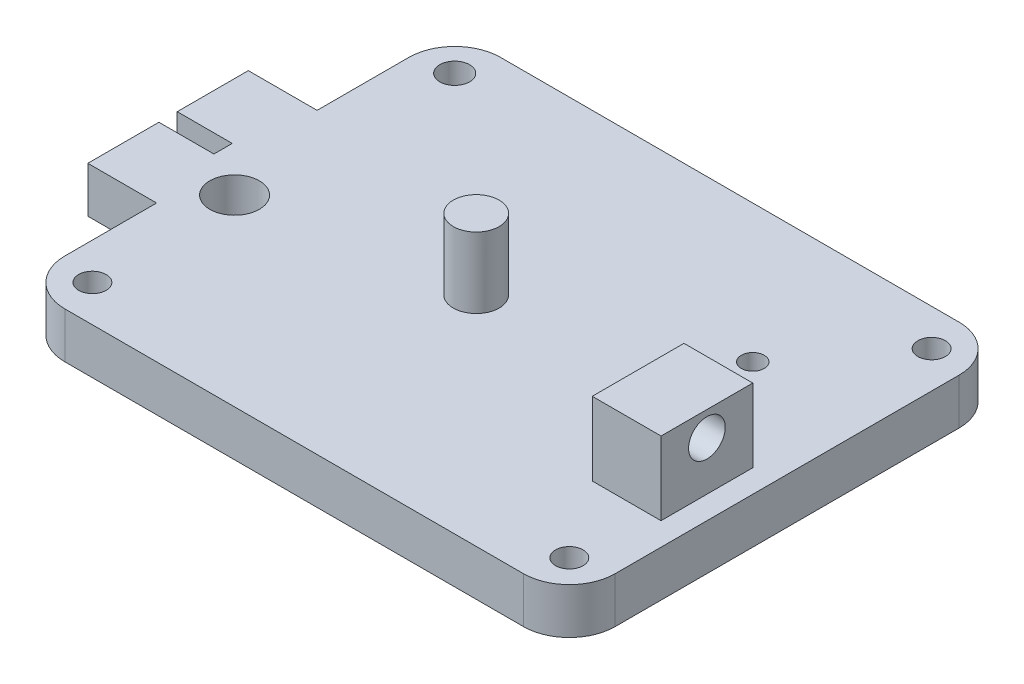
SolidWorks part; units mm, degrees
ref_plane "Front Plane" through (0, 0, 0) normal (0, 0, 1) x (1, 0, 0)
ref_plane "Top Plane" through (0, 0, 0) normal (0, 1, 0) x (1, 0, 0)
ref_plane "Right Plane" through (0, 0, 0) normal (1, 0, 0) x (0, 0, -1)
sketch "Sketch1" plane through (0, 0, 0) normal (0, 1, 0) x (1, 0, 0)
  line L1 (0, 0) -> (120, 0)
  line L2 (0, 0) -> (0, 95)
  line L3 (0, 95) -> (120, 95)
  line L4 (120, 0) -> (120, 95)
  dimension "D1" = 120
  dimension "Sketch 2" = 95
extrude "Boss-Extrude1" add sketch "Sketch1" along normal blind 10
fillet "Fillet1" radius 10 4 edges at (0, 5, 0) (0, 5, -95) (120, 5, -95) (120, 5, 0)
sketch "Sketch3" plane through (0, 10, 0) normal (0, 1, 0) x (1, 0, 0)
  line L1 (110, 95) -> (10, 95) construction
  line L2 (0, 85) -> (0, 10) construction
  circle A0 centre (52.2, 47.5) radius 5
  dimension "D3" = 10
  dimension "D1" = 47.5
  dimension "D2" = 52.2
extrude "Boss-Extrude3" add sketch "Sketch3" along normal blind 15.4
sketch "Sketch4" plane through (0, 10, 0) normal (0, 1, 0) x (1, 0, 0)
  line L0 (120, 10) -> (120, 85) construction
  line L1 (100, 25) -> (115, 25)
  line L2 (100, 25) -> (100, 45)
  line L3 (100, 45) -> (115, 45)
  line L4 (115, 25) -> (115, 45)
  line L6 (10, 0) -> (110, 0) construction
  dimension "D1" = 5
  dimension "D2" = 25
  dimension "D3" = 15
  dimension "D4" = 20
extrude "Boss-Extrude4" add sketch "Sketch4" along normal blind 16
sketch "Sketch5" plane through (0, 0, 0) normal (-1, 0, 0) x (0, 0, 1)
  line L0 (-85, 10) -> (-10, 10) construction
  line L1 (-65, 10) -> (-30, 10)
  line L2 (-65, 10) -> (-65, 0)
  line L3 (-65, 0) -> (-30, 0)
  line L4 (-30, 10) -> (-30, 0)
  line L5 (-85, 0) -> (-10, 0) construction
  line L8 (-85, 10) -> (-85, 0) construction
  line L9 (-10, 0) -> (-10, 10) construction
  dimension "D1" = 20
  dimension "D2" = 20
extrude "Boss-Extrude5" add sketch "Sketch5" along normal blind 15
sketch "Sketch6" plane through (0, 10, 0) normal (0, 1, 0) x (1, 0, 0)
  line L0 (-15, 30) -> (-15, 65) construction
  line L1 (-15, 49.5) -> (-3, 49.5)
  line L3 (-15, 45.5) -> (-3, 45.5)
  line L4 (-3, 49.5) -> (-3, 45.5)
  line L5 (-15, 47.5) -> (-3, 45.5) construction
  line L6 (-15, 47.5) -> (-3, 49.5) construction
  line L8 (-15, 49.5) -> (-15, 45.5)
  point P0 (-15, 47.5)
  dimension "D1" = 12
  dimension "D2" = 4
extrude "Cut-Extrude1" cut sketch "Sketch6" against normal through all
sketch "Sketch8" plane through (0, 10, 0) normal (0, 1, 0) x (1, 0, 0)
  line L0 (10, 0) -> (110, 0) construction
  line L1 (0, 30) -> (0, 10) construction
  circle A0 centre (7, 40) radius 5.4
  dimension "D1" = 10.8
  dimension "D2" = 40
  dimension "D3" = 7
extrude "Cut-Extrude3" cut sketch "Sketch8" against normal through all
sketch "Sketch9" plane through (0, 10, 0) normal (0, 1, 0) x (1, 0, 0)
  line L0 (110, 95) -> (10, 95) construction
  line L1 (120, 10) -> (120, 85) construction
  circle A0 centre (95, 65) radius 2.5
  dimension "D1" = 5
  dimension "D2" = 30
  dimension "D3" = 25
extrude "Cut-Extrude4" cut sketch "Sketch9" against normal through all
sketch "Sketch10" plane through (115, 0, 0) normal (1, 0, 0) x (0, 0, -1)
  circle A0 centre (35.0007, 20.6547) radius 4
  dimension "8" = 8
extrude "Cut-Extrude5" cut sketch "Sketch10" against normal up to next
sketch "Sketch11" plane through (0, 10, 0) normal (0, 1, 0) x (1, 0, 0)
  line L0 (10, 0) -> (110, 0) construction
  line L1 (8, 8) -> (112, 8) construction
  line L2 (8, 8) -> (8, 87) construction
  line L3 (8, 87) -> (112, 87) construction
  line L4 (112, 8) -> (112, 87) construction
  line L5 (110, 95) -> (10, 95) construction
  line L6 (0, 85) -> (0, 65) construction
  line L7 (120, 10) -> (120, 85) construction
  circle A0 centre (8, 87) radius 3.25
  circle A1 centre (112, 87) radius 3
  circle A2 centre (8, 8) radius 3
  circle A3 centre (112, 8) radius 3
  dimension "D5" = 6.5
  dimension "D1" = 8
  dimension "D2" = 8
  dimension "D3" = 8
  dimension "D4" = 8
extrude "Cut-Extrude6" cut sketch "Sketch11" against normal through all
sketch "Sketch12" plane through (0, 0, 0) normal (0, -1, 0) x (1, 0, 0)
  line L0 (-3, -47.5) -> (54.464, -47.5) construction
  line L1 (-3, -45.5) -> (-3, -49.5) construction
  line L2 (54.464, -57.5) -> (54.464, -37.5) construction
  circle A0 centre (54.464, -37.5) radius 2.5
  circle A1 centre (54.464, -57.5) radius 2.65
  point P8 (54.464, -47.5)
  dimension "D2" = 5
  dimension "D3" = 5.3
  dimension "D1" = 20
extrude "Cut-Extrude7" cut sketch "Sketch12" against normal blind 5
